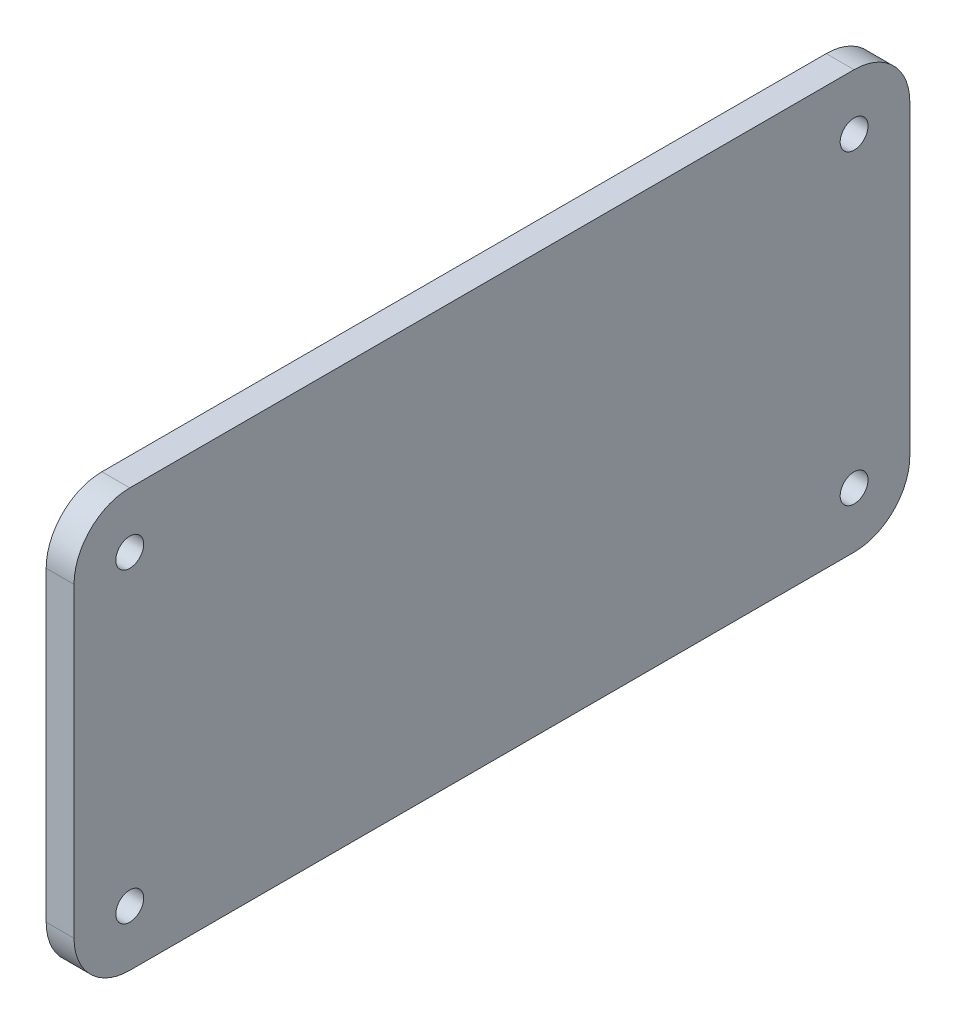
SolidWorks part; units mm, degrees
material "Acrylic (Medium-high impact)"
ref_plane "Front Plane" through (0, 0, 0) normal (0, 0, 1) x (1, 0, 0)
ref_plane "Top Plane" through (0, 0, 0) normal (0, 1, 0) x (1, 0, 0)
ref_plane "Right Plane" through (0, 0, 0) normal (1, 0, 0) x (0, 0, -1)
sketch "Sketch1" plane through (0, 0, 0) normal (1, 0, 0) x (0, 0, -1)
  line L0 (-51.7638, -0.9328) -> (41.9994, -0.9328) construction
  line L2 (-65, 37.5) -> (65, 37.5)
  line L3 (-75, 27.5) -> (-75, -27.5)
  line L4 (-65, -37.5) -> (65, -37.5)
  line L5 (75, 27.5) -> (75, -27.5)
  line L6 (-75, 37.5) -> (75, -37.5) construction
  line L7 (-75, -37.5) -> (75, 37.5) construction
  arc A0 (75, 27.5) -> (65, 37.5) centre (65, 27.5) ccw
  arc A1 (75, -27.5) -> (65, -37.5) centre (65, -27.5) cw
  arc A2 (-65, 37.5) -> (-75, 27.5) centre (-65, 27.5) ccw
  arc A3 (-75, -27.5) -> (-65, -37.5) centre (-65, -27.5) ccw
  circle A4 centre (-65, 27.5) radius 2.5
  circle A5 centre (65, 27.5) radius 2.5
  circle A6 centre (65, -27.5) radius 2.5
  circle A7 centre (-65, -27.5) radius 2.5
  point P2 (0, 0)
  dimension "D3" = 10
  dimension "5mm" = 5
  dimension "D1" = 150
  dimension "D2" = 75
extrude "Boss-Extrude1" add sketch "Sketch1" along normal blind 5
sketch "Sketch2" plane through (5, 0, 0) normal (1, 0, 0) x (0, 0, -1)
  line L0 (-34.29, 26.67) -> (30.226, 26.67) construction
  line L1 (30.226, 26.67) -> (31.75, 25.146) construction
  line L2 (31.75, 13.716) -> (34.29, 11.176) construction
  line L3 (34.29, 11.176) -> (34.29, -21.59) construction
  line L4 (34.29, -21.59) -> (31.75, -24.13) construction
  line L5 (31.75, -24.13) -> (31.75, -26.67)
  line L6 (31.75, -26.67) -> (-34.29, -26.67) construction
  line L7 (-34.29, -26.67) -> (-34.29, 26.67) construction
  line L8 (31.75, 25.146) -> (31.75, 13.716) construction
  line L9 (34.2265, 26.6065) -> (34.2265, -26.67) construction
  line L10 (-34.2265, 26.67) -> (34.2265, -26.67) construction
  line L11 (-34.29, -26.6065) -> (34.2265, 26.6065) construction
  line L12 (72.0711, 34.5711) -> (-72.0711, -34.5711) construction
  line L13 (72.0711, -34.5711) -> (-72.0711, 34.5711) construction
  arc A0 (30.226, 26.6065) -> (30.1811, 26.6251) centre (30.226, 26.67) ccw
  arc A1 (-34.2265, 26.67) -> (-34.29, 26.6065) centre (-34.29, 26.67) ccw
  arc A2 (31.7051, 25.1011) -> (31.6865, 25.146) centre (31.75, 25.146) ccw
  arc A3 (34.2451, 11.1311) -> (34.2265, 11.176) centre (34.29, 11.176) ccw
  arc A4 (34.2265, -21.59) -> (34.2451, -21.5451) centre (34.29, -21.59) ccw
  arc A5 (31.8135, -24.13) -> (31.7949, -24.1749) centre (31.75, -24.13) ccw
  arc A6 (31.6865, -26.67) -> (31.75, -26.6065) centre (31.75, -26.67) ccw
  arc A7 (-34.29, -26.6065) -> (-34.2265, -26.67) centre (-34.29, -26.67) ccw
  circle A8 centre (31.75, 8.89) radius 1.6
  circle A9 centre (31.75, -19.05) radius 1.6
  circle A10 centre (-19.05, 24.13) radius 1.6
  circle A11 centre (-20.32, -24.13) radius 1.6
  dimension "D3" = 3.2
  dimension "D6" = 3.2
  dimension "D9" = 3.2
  dimension "D11" = 3.2
  dimension "D1" = 15.24
  dimension "D2" = 2.54
  dimension "D4" = 2.54
  dimension "D5" = 13.97
  dimension "D7" = 17.78
  dimension "D8" = 2.54
  dimension "D10" = 2.54
  dimension "D12" = 53.34
  dimension "D13" = 64.516
  dimension "D14" = 66.04
extrude "Cut-Extrude1" [suppressed] cut sketch "Sketch2" against normal through all contours A11 | A9 | A8 | A10
